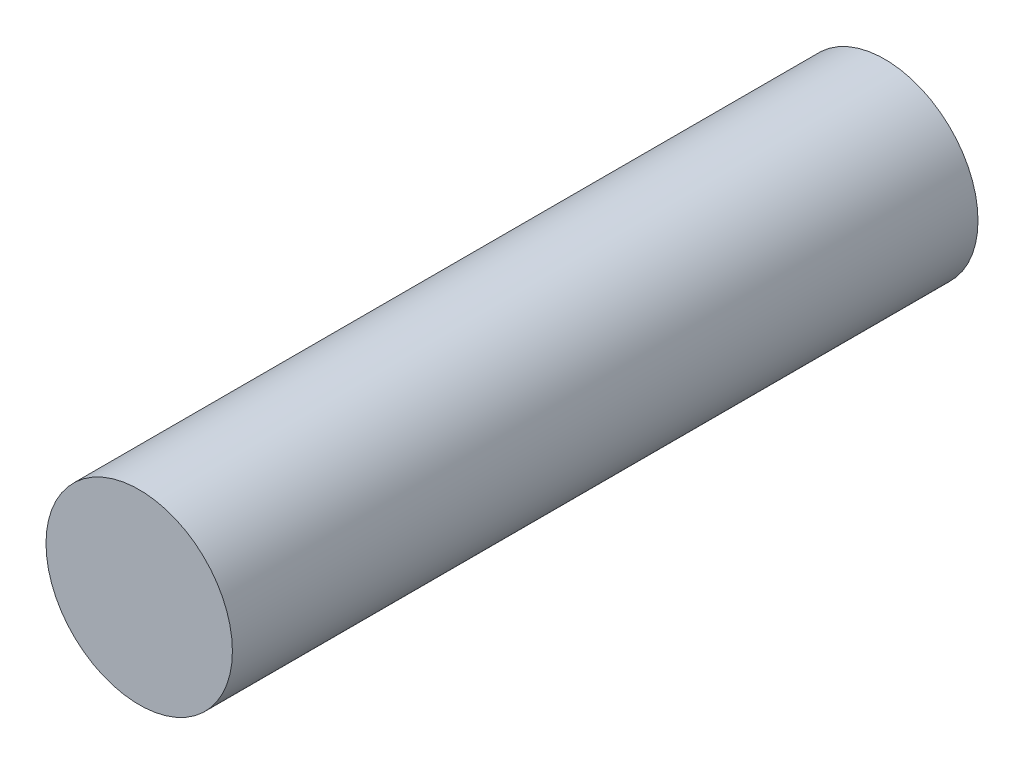
SolidWorks part; units mm, degrees
ref_plane "Front Plane" through (0, 0, 0) normal (0, 0, 1) x (1, 0, 0)
ref_plane "Top Plane" through (0, 0, 0) normal (0, 1, 0) x (1, 0, 0)
ref_plane "Right Plane" through (0, 0, 0) normal (1, 0, 0) x (0, 0, -1)
sketch "Sketch1" plane through (0, 0, 0) normal (0, 0, 1) x (1, 0, 0)
  circle A0 centre (0, 0) radius 1
  dimension "D1" = 2
extrude "Boss-Extrude1" add sketch "Sketch1" along normal blind 8
